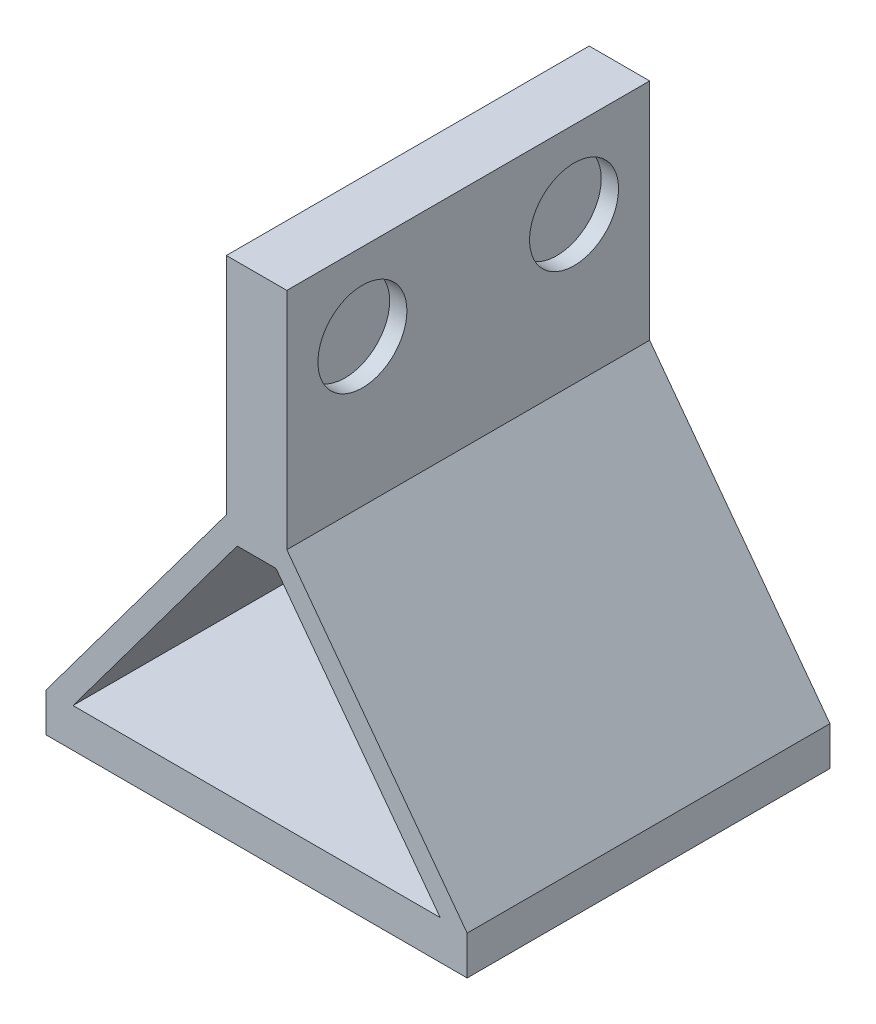
SolidWorks part; units mm, degrees
ref_plane "Front Plane" through (0, 0, 0) normal (0, 0, 1) x (1, 0, 0)
ref_plane "Top Plane" through (0, 0, 0) normal (0, 1, 0) x (1, 0, 0)
ref_plane "Right Plane" through (0, 0, 0) normal (1, 0, 0) x (0, 0, -1)
sketch "Sketch1" plane through (0, 0, 0) normal (0, 0, 1) x (1, 0, 0)
  line L0 (-0.5471, -2.4844) -> (-0.5471, 25.5156) construction
  line L2 (-24.9221, -2.4844) -> (-24.9221, -4.9844)
  line L3 (-24.9221, -4.9844) -> (23.8279, -4.9844)
  line L4 (23.8279, -2.4844) -> (23.8279, -4.9844)
  line L5 (-4.0471, 25.5156) -> (2.9529, 25.5156)
  line L6 (-4.0471, 25.5156) -> (-24.9221, -2.4844)
  line L7 (2.9529, 25.5156) -> (23.8279, -2.4844)
  line L8 (-21.8038, -2.4844) -> (-2.7926, 23.0156)
  line L9 (-2.7926, 23.0156) -> (1.6984, 23.0156)
  line L10 (1.6984, 23.0156) -> (20.7096, -2.4844)
  line L11 (-21.8038, -2.4844) -> (20.7096, -2.4844)
  point P9 (-0.5471, 25.5156)
  dimension "D1" = 48.75
  dimension "D2" = 2.5
  dimension "D3" = 7
  dimension "D4" = 2.5
  dimension "D5" = 2.5
  dimension "D6" = 2.5
  dimension "D7" = 2.5
extrude "Boss-Extrude1" add sketch "Sketch1" along normal blind 42
sketch "Sketch2" plane through (0, 0, 42) normal (0, 0, 1) x (1, 0, 0)
  line L1 (-4.0471, 25.5156) -> (2.9529, 25.5156)
  line L2 (-4.0471, 25.5156) -> (-4.0471, 51.5156)
  line L3 (-4.0471, 51.5156) -> (2.9529, 51.5156)
  line L4 (2.9529, 25.5156) -> (2.9529, 51.5156)
  dimension "D1" = 26
extrude "Boss-Extrude2" add sketch "Sketch2" against normal blind 42
sketch "Sketch3" plane through (2.9529, 0, 0) normal (1, 0, 0) x (0, 0, -1)
  line L0 (-42, 25.5156) -> (0, 25.5156) construction
  line L1 (-42, 25.5156) -> (-42, 51.5156) construction
  circle A0 centre (-33.25, 42.5156) radius 5.15
  circle A1 centre (-8.75, 42.5156) radius 5.15
  dimension "D1" = 17
  dimension "D3" = 8.75
  dimension "D2" = 2
extrude "Cut-Extrude1" cut sketch "Sketch3" against normal blind 2
sketch "Sketch4" plane through (0, -4.9844, 0) normal (0, -1, 0) x (1, 0, 0)
  line L0 (-24.9221, 42) -> (23.8279, 42) construction
  line L2 (-24.9221, 42) -> (-24.9221, 0) construction
  circle A0 centre (-12.9221, 33.4) radius 3.25
  circle A1 centre (11.8779, 33.4) radius 3.25
  circle A2 centre (11.8779, 8.6) radius 3.25
  circle A3 centre (-12.9221, 8.6) radius 3.25
  dimension "D1" = 2
  dimension "D3" = 8.6
  dimension "D4" = 12
  dimension "D2" = 2
extrude "Boss-Extrude3" add sketch "Sketch4" along normal blind 7
sketch "Sketch5" plane through (0, 0, 42) normal (0, 0, 1) x (1, 0, 0)
  line L1 (-24.9221, -4.9844) -> (23.8279, -4.9844)
  line L2 (-24.9221, -4.9844) -> (-24.9221, -6.9844)
  line L3 (-24.9221, -6.9844) -> (23.8279, -6.9844)
  line L4 (23.8279, -4.9844) -> (23.8279, -6.9844)
  dimension "D1" = 2
extrude "Boss-Extrude4" add sketch "Sketch5" against normal blind 42
